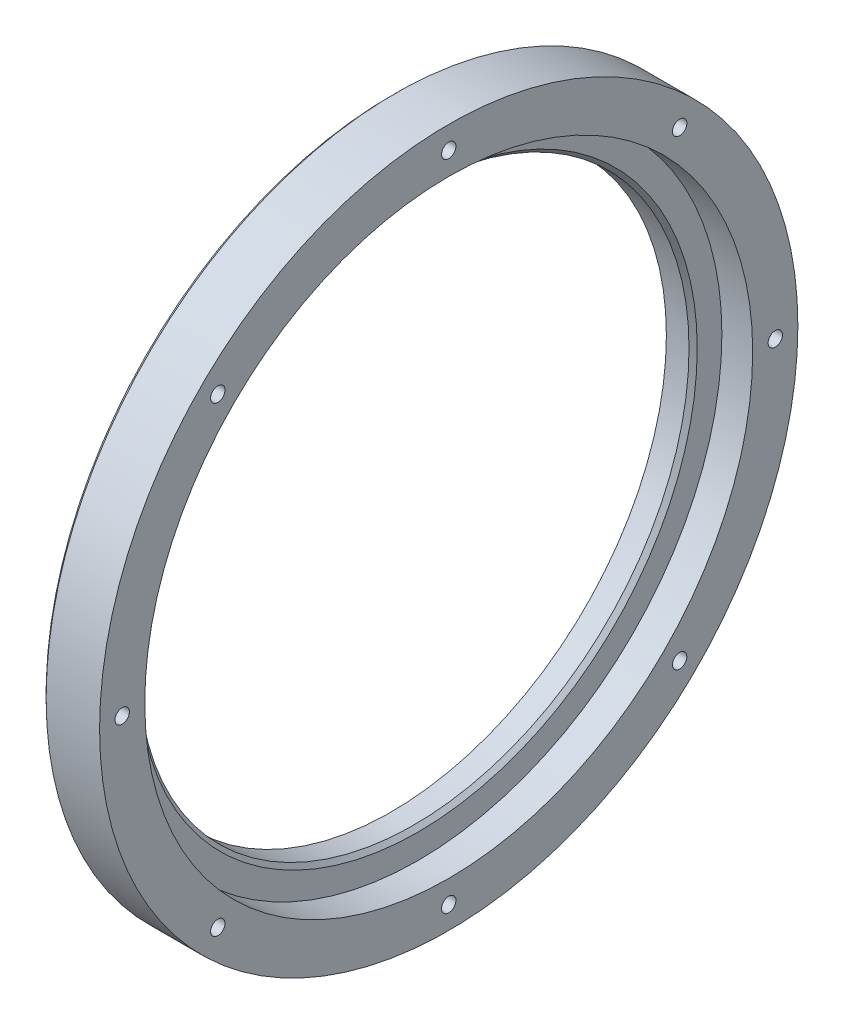
SolidWorks part; units mm, degrees
ref_plane "Płaszczyzna przednia" through (0, 0, 0) normal (0, 0, 1) x (1, 0, 0)
ref_plane "Płaszczyzna górna" through (0, 0, 0) normal (0, 1, 0) x (1, 0, 0)
ref_plane "Płaszczyzna prawa" through (0, 0, 0) normal (1, 0, 0) x (0, 0, -1)
sketch "Szkic1" plane through (0, 0, 0) normal (0, 0, 1) x (1, 0, 0)
  line L0 (-272.858, 75.0093) -> (-280.358, 75.0093)
  line L1 (-272.858, -79.75) -> (-272.858, 79.75) construction
  line L2 (-272.858, 86.0093) -> (-272.858, -83.9907) construction
  line L3 (-280.358, 75.0093) -> (-280.358, 68.0093)
  line L4 (-280.358, 68.0093) -> (-286.8712, 68.0093)
  line L5 (-286.8712, 68.0093) -> (-286.8712, 85.0093)
  line L6 (-285.8712, 86.0093) -> (-272.858, 86.0093)
  line L7 (-252.858, 86.0093) -> (-272.858, 86.0093) construction
  line L8 (-268.908, 1.0093) -> (-389.244, 1.0093) construction
  line L10 (-286.8712, 85.0093) -> (-285.8712, 86.0093)
  line L11 (-279.858, -79.2) -> (-279.858, 79.2) construction
  line L12 (-272.858, 75.0093) -> (-272.858, 86.0093)
  point P4 (-286.8712, 86.0093)
  dimension "D1" = 1.5
  dimension "D4" = 1
  dimension "D2" = 18
  dimension "D3" = 0.5
  dimension "D5" = 1
revolve "Obrót1" add sketch "Szkic1" angle 360 about L8
sketch "Szkic2" plane through (-286.8712, 0, 0) normal (-1, 0, 0) x (0, 0, 1)
  line L0 (0, 1.0093) -> (67, 1.0093) construction
  line L1 (74, 1.0093) -> (85, 1.0093) construction
  line L2 (0, 1.0093) -> (47.3762, -46.3669) construction
  line L3 (52.3259, -51.3166) -> (60.1041, -59.0948) construction
  line L4 (0, 1.0093) -> (0, -65.9907) construction
  line L5 (0, -72.9907) -> (0, -83.9907) construction
  line L6 (0, 1.0093) -> (-47.3762, -46.3669) construction
  line L7 (-52.3259, -51.3166) -> (-60.1041, -59.0948) construction
  line L8 (0, 1.0093) -> (-67, 1.0093) construction
  line L9 (-74, 1.0093) -> (-85, 1.0093) construction
  line L10 (0, 1.0093) -> (-47.3762, 48.3854) construction
  line L11 (-52.3259, 53.3352) -> (-60.1041, 61.1133) construction
  line L12 (0, 1.0093) -> (0, 68.0093) construction
  line L13 (0, 75.0093) -> (0, 86.0093) construction
  line L14 (0, 1.0093) -> (47.3762, 48.3854) construction
  line L15 (52.3259, 53.3352) -> (60.1041, 61.1133) construction
  circle A0 centre (0, 1.0093) radius 85 construction
  circle A1 centre (79.5, 1.0093) radius 1.75
  circle A2 centre (59.9476, 1.0093) radius 1.75 construction
  circle A3 centre (0, 1.0093) radius 74 construction
  circle A4 centre (0, 1.0093) radius 67 construction
  circle A5 centre (56.215, -55.2057) radius 1.75
  circle A6 centre (0, -78.4907) radius 1.75
  circle A7 centre (-56.215, -55.2057) radius 1.75
  circle A8 centre (-79.5, 1.0093) radius 1.75
  circle A9 centre (-56.215, 57.2243) radius 1.75
  circle A10 centre (0, 80.5093) radius 1.75
  circle A11 centre (56.215, 57.2243) radius 1.75
  point P58 (0, 1.0093)
extrude "Wytnij-wyciągnięcie1" cut sketch "Szkic2" against normal through all
sketch "Szkic4" plane through (-286.8712, 0, 0) normal (-1, 0, 0) x (0, 0, 1)
  line L0 (0, 1.0093) -> (91.9385, 1.0093) construction
  line L1 (0, 1.0093) -> (65.0103, -64.0011) construction
  line L2 (0, 1.0093) -> (0, -90.9292) construction
  line L3 (0, 1.0093) -> (-65.0103, -64.0011) construction
  line L4 (0, 1.0093) -> (-91.9385, 1.0093) construction
  line L5 (0, 1.0093) -> (-65.0103, 66.0196) construction
  line L6 (0, 1.0093) -> (0, 92.9478) construction
  line L7 (0, 1.0093) -> (65.0103, 66.0196) construction
  circle A0 centre (79.5, 1.0093) radius 3
  circle A1 centre (59.9476, 1.0093) radius 3 construction
  circle A2 centre (56.215, -55.2057) radius 3
  circle A3 centre (0, -78.4907) radius 3
  circle A4 centre (-56.215, -55.2057) radius 3
  circle A5 centre (-79.5, 1.0093) radius 3
  circle A6 centre (-56.215, 57.2243) radius 3
  circle A7 centre (0, 80.5093) radius 3
  circle A8 centre (56.215, 57.2243) radius 3
  point P32 (0, 1.0093)
extrude "Wytnij-wyciągnięcie2" cut sketch "Szkic4" against normal blind 4
chamfer "Sfazowanie1" distance 1 angle 45 1 edges at (-280.358, 1.0093, -67)
move or copy body "Obiekt-Przenieś/Kopiuj1" [suppressed] bodies to move or copy 103 copy no rotation origin (-139.9323, 1.0093, 139.9323) rotation axis (0.7071, 0, 0.7071) rotation angle 180
